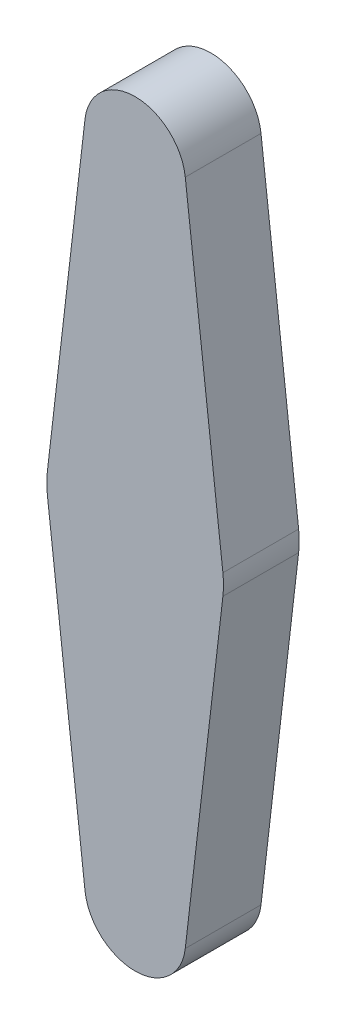
SolidWorks part; units mm, degrees
ref_plane "前视基准面" through (0, 0, 0) normal (0, 0, 1) x (1, 0, 0)
ref_plane "上视基准面" through (0, 0, 0) normal (0, 1, 0) x (1, 0, 0)
ref_plane "右视基准面" through (0, 0, 0) normal (1, 0, 0) x (0, 0, -1)
sketch "草图1" plane through (0, 0, 0) normal (0, 0, 1) x (1, 0, 0)
  line L0 (0, 0) -> (0, 13) construction
  line L1 (-1.9866, 13.2308) -> (-3.4766, 0.4038)
  line L2 (1.9866, 13.2308) -> (3.4766, 0.4038)
  line L4 (1.9866, -13.2308) -> (3.4766, -0.4038)
  line L5 (-1.9866, -13.2308) -> (-3.4766, -0.4038)
  arc A0 (-3.4766, 0.4038) -> (-3.4766, -0.4038) centre (0, 0) ccw
  arc A1 (1.9866, 13.2308) -> (-1.9866, 13.2308) centre (0, 13) ccw
  arc A2 (1.9866, -13.2308) -> (-1.9866, -13.2308) centre (0, -13) cw
  arc A3 (3.4766, -0.4038) -> (3.4766, 0.4038) centre (0, 0) ccw
  dimension "D1" = 7
  dimension "D2" = 4
  dimension "D4" = 2
  dimension "D3" = 13
extrude "凸台-拉伸1" add sketch "草图1" along normal blind 3
